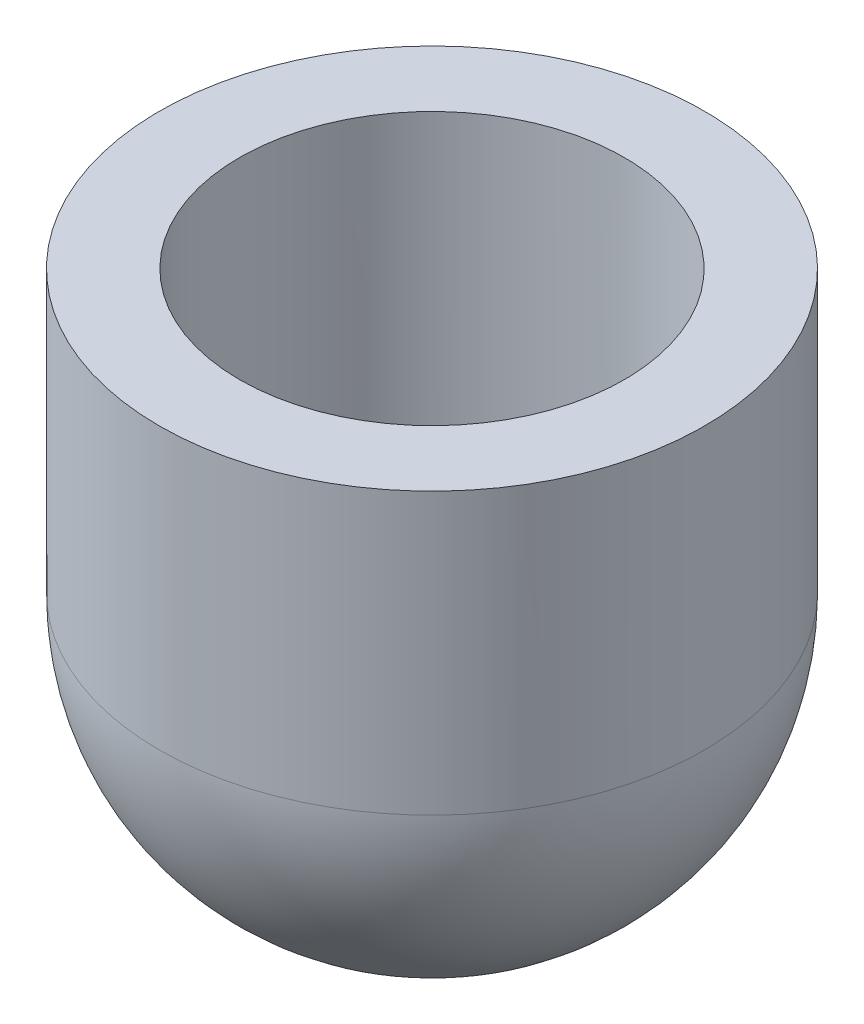
SolidWorks part; units mm, degrees
ref_plane "Front Plane" through (0, 0, 0) normal (0, 0, 1) x (1, 0, 0)
ref_plane "Top Plane" through (0, 0, 0) normal (0, 1, 0) x (1, 0, 0)
ref_plane "Right Plane" through (0, 0, 0) normal (1, 0, 0) x (0, 0, -1)
sketch "Sketch1" plane through (0, 0, 0) normal (1, 0, 0) x (0, 0, -1)
  line L0 (8.636, 0) -> (6.096, 0)
  line L1 (0, -14.986) -> (0, -17.526)
  line L2 (8.636, 0) -> (8.636, -8.89)
  line L3 (0, 26.3769) -> (0, 0) construction
  line L4 (6.096, 0) -> (6.096, -8.89)
  line L5 (0, -14.986) -> (0, -44.37) construction
  arc A1 (8.636, -8.89) -> (0, -17.526) centre (0, -8.89) cw
  arc A2 (6.096, -8.89) -> (0, -14.986) centre (0, -8.89) cw
  dimension "D5" = 6.096
  dimension "D1" = 17.526
  dimension "D2" = 8.636
  dimension "D3" = 2.54
  dimension "D4" = 8.89
  dimension "D6" = 14.986
  dimension "D7" = 6.096
revolve "Revolve1" add sketch "Sketch1" angle 360 about L3
